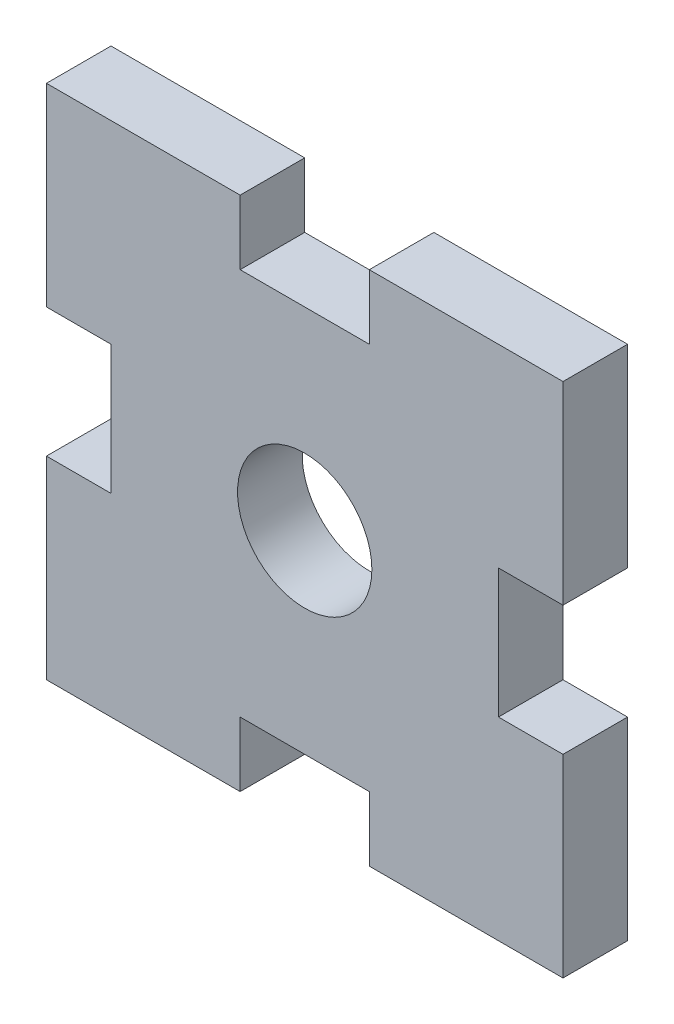
SolidWorks part; units mm, degrees
ref_plane "Front Plane" through (0, 0, 0) normal (0, 0, 1) x (1, 0, 0)
ref_plane "Top Plane" through (0, 0, 0) normal (0, 1, 0) x (1, 0, 0)
ref_plane "Right Plane" through (0, 0, 0) normal (1, 0, 0) x (0, 0, -1)
sketch "Sketch1" plane through (0, 0, 0) normal (0, 0, 1) x (1, 0, 0)
  line L0 (0, -31.75) -> (0, 31.75) construction
  line L1 (-12.7, 12.7) -> (-3.175, 12.7)
  line L2 (-12.7, 12.7) -> (-12.7, 3.175)
  line L3 (0, 0) -> (35.3222, 0) construction
  line L4 (-9.525, -3.175) -> (-12.7, -3.175)
  line L5 (-12.7, -3.175) -> (-12.7, -12.7)
  line L6 (-12.7, 3.175) -> (-9.525, 3.175)
  line L7 (-9.525, 3.175) -> (-9.525, -3.175)
  line L8 (-12.7, -12.7) -> (-3.175, -12.7)
  line L9 (12.7, 12.7) -> (12.7, 3.175)
  line L10 (12.7, 12.7) -> (3.175, 12.7)
  line L11 (12.7, 3.175) -> (9.525, 3.175)
  line L12 (-3.175, -12.7) -> (-3.175, -9.525)
  line L13 (-3.175, -9.525) -> (3.175, -9.525)
  line L14 (3.175, -9.525) -> (3.175, -12.7)
  line L15 (3.175, -12.7) -> (12.7, -12.7)
  line L16 (9.525, 3.175) -> (9.525, -3.175)
  line L17 (9.525, -3.175) -> (12.7, -3.175)
  line L18 (12.7, -12.7) -> (12.7, -3.175)
  line L22 (-3.175, 12.7) -> (-3.175, 9.525)
  line L23 (-3.175, 9.525) -> (3.175, 9.525)
  line L24 (3.175, 9.525) -> (3.175, 12.7)
  circle A0 centre (0, 0) radius 3.302
  point P18 (-38.1, 0)
  point P26 (38.1, 0)
  dimension "D3" = 12.7
  dimension "D1" = 3.175
  dimension "D2" = 3.175
  dimension "D4" = 6.35
  dimension "D5" = 25.4
  dimension "D6" = 3.175
  dimension "D7" = 6.35
  dimension "D8" = 3.175
  dimension "D9" = 12.7
  dimension "D10" = 3.175
extrude "Extrude1" add sketch "Sketch1" along normal blind 3.175
